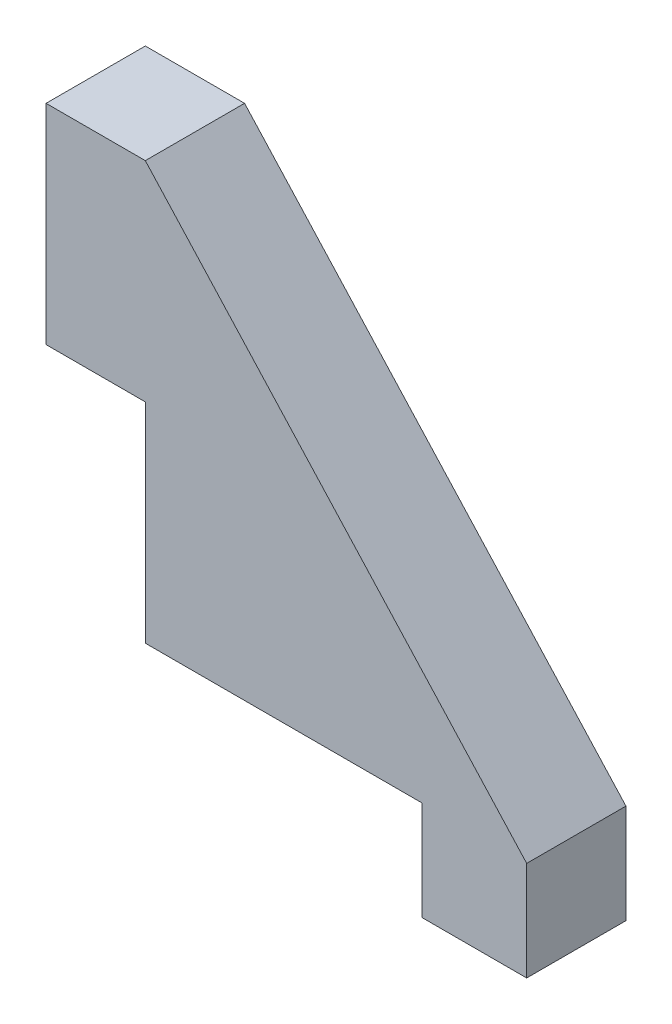
SolidWorks part; units mm, degrees
material "Pine"
ref_plane "Front Plane" through (0, 0, 0) normal (0, 0, 1) x (1, 0, 0)
ref_plane "Top Plane" through (0, 0, 0) normal (0, 1, 0) x (1, 0, 0)
ref_plane "Right Plane" through (0, 0, 0) normal (1, 0, 0) x (0, 0, -1)
sketch "Sketch1" plane through (0, 0, 0) normal (0, 0, 1) x (1, 0, 0)
  line L0 (0, 0) -> (0, 10)
  line L1 (0, 20) -> (18.25, 0)
  line L2 (13.25, 0) -> (0, 0)
  line L4 (0, 20) -> (-4.75, 20)
  line L6 (0, 10) -> (-4.75, 10)
  line L7 (-4.75, 20) -> (-4.75, 10)
  line L9 (18.25, 0) -> (18.25, -4.75)
  line L10 (18.25, -4.75) -> (13.25, -4.75)
  line L11 (13.25, 0) -> (13.25, -4.75)
  dimension "D1" = 23
  dimension "D2" = 10
  dimension "D3" = 10
  dimension "D4" = 4.75
  dimension "D5" = 5
  dimension "D6" = 4.75
extrude "Boss-Extrude1" add sketch "Sketch1" along normal blind 4.75
